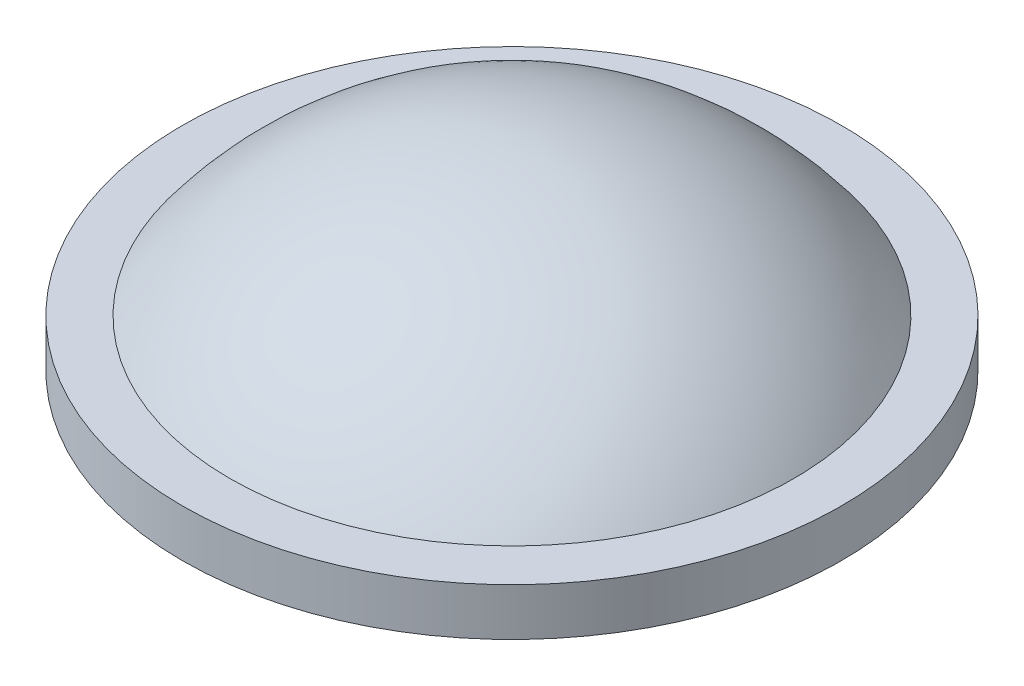
SolidWorks part; units mm, degrees
material "PC High Viscosity"
ref_plane "Front Plane" through (0, 0, 0) normal (0, 0, 1) x (1, 0, 0)
ref_plane "Top Plane" through (0, 0, 0) normal (0, 1, 0) x (1, 0, 0)
ref_plane "Right Plane" through (0, 0, 0) normal (1, 0, 0) x (0, 0, -1)
sketch "Sketch1" plane through (0, 0, 0) normal (1, 0, 0) x (0, 0, -1)
  line L0 (0, 0) -> (-6.25, 0)
  line L1 (-6.25, 0) -> (-6.25, 0.9)
  line L2 (-6.25, 0.9) -> (-5.35, 0.9)
  line L3 (0, 3.6) -> (0, 0) construction
  line L4 (0, 0) -> (0, 3.6)
  arc A0 (-5.35, 0.9) -> (0, 3.6) centre (0, -3.0505) cw
  dimension "D1" = 6.25
  dimension "D2" = 0.9
  dimension "D3" = 5.35
  dimension "D4" = 3.6
revolve "Revolve1" add sketch "Sketch1" angle 360 about L3
